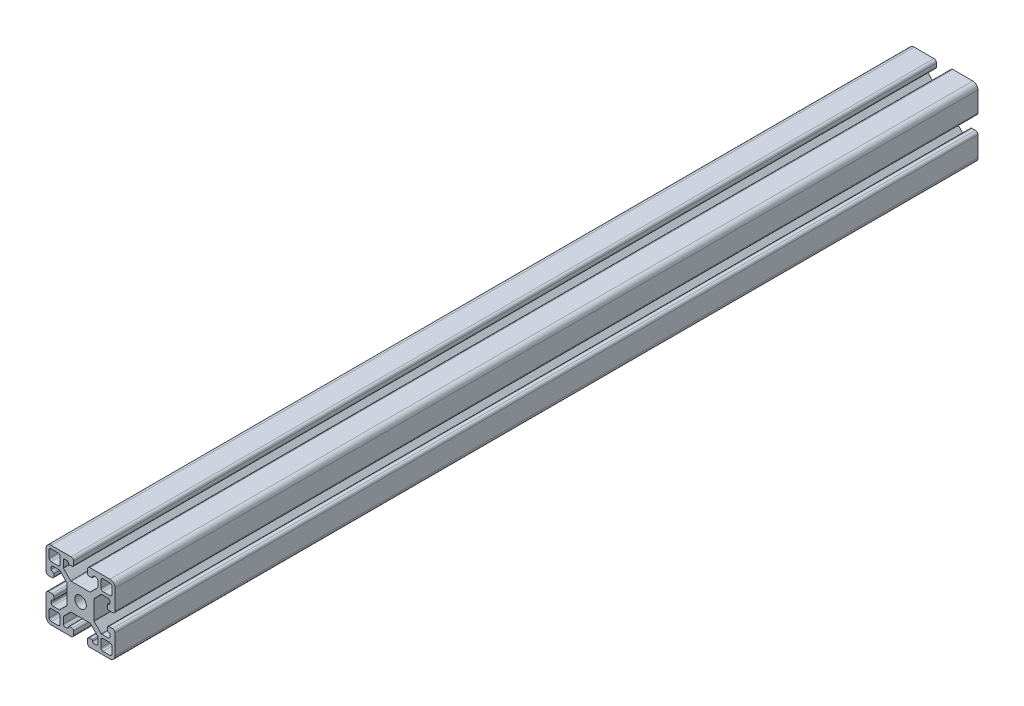
SolidWorks part; units mm, degrees
ref_plane "Front Plane" through (0, 0, 0) normal (0, 0, 1) x (1, 0, 0)
ref_plane "Top Plane" through (0, 0, 0) normal (0, 1, 0) x (1, 0, 0)
ref_plane "Right Plane" through (0, 0, 0) normal (1, 0, 0) x (0, 0, -1)
sketch "Sketch1" plane through (0, 0, 0) normal (0, 0, 1) x (1, 0, 0)
  line B0 (-17, 11.78) -> (-13, 11.78)
  arc B1 (-13, 11.78) -> (-11.78, 13) centre (-13, 13) ccw
  line B2 (-11.78, 13) -> (-11.78, 17)
  arc B3 (-11.78, 17) -> (-13, 18.22) centre (-13, 17) ccw
  line B4 (-13, 18.22) -> (-17, 18.22)
  arc B5 (-17, 18.22) -> (-18.22, 17) centre (-17, 17) ccw
  line B6 (-18.22, 17) -> (-18.22, 13)
  arc B7 (-18.22, 13) -> (-17, 11.78) centre (-17, 13) ccw
  line B8 (-18.22, -13) -> (-18.22, -17)
  arc B9 (-18.22, -17) -> (-17, -18.22) centre (-17, -17) ccw
  line B10 (-17, -18.22) -> (-13, -18.22)
  arc B11 (-13, -18.22) -> (-11.78, -17) centre (-13, -17) ccw
  line B12 (-11.78, -17) -> (-11.78, -13)
  arc B13 (-11.78, -13) -> (-13, -11.78) centre (-13, -13) ccw
  line B14 (-13, -11.78) -> (-17, -11.78)
  arc B15 (-17, -11.78) -> (-18.22, -13) centre (-17, -13) ccw
  line B16 (13, -18.22) -> (17, -18.22)
  arc B17 (17, -18.22) -> (18.22, -17) centre (17, -17) ccw
  line B18 (18.22, -17) -> (18.22, -13)
  arc B19 (18.22, -13) -> (17, -11.78) centre (17, -13) ccw
  line B20 (17, -11.78) -> (13, -11.78)
  arc B21 (13, -11.78) -> (11.78, -13) centre (13, -13) ccw
  line B22 (11.78, -13) -> (11.78, -17)
  arc B23 (11.78, -17) -> (13, -18.22) centre (13, -17) ccw
  line B24 (18.22, 13) -> (18.22, 17)
  arc B25 (18.22, 17) -> (17, 18.22) centre (17, 17) ccw
  line B26 (17, 18.22) -> (13, 18.22)
  arc B27 (13, 18.22) -> (11.78, 17) centre (13, 17) ccw
  line B28 (11.78, 17) -> (11.78, 13)
  arc B29 (11.78, 13) -> (13, 11.78) centre (13, 13) ccw
  line B30 (13, 11.78) -> (17, 11.78)
  arc B31 (17, 11.78) -> (18.22, 13) centre (17, 13) ccw
  line B32 (-9.8536, -11.9786) -> (-5.7714, -7.8964)
  arc B33 (-5.4179, -7.75) -> (-5.7714, -7.8964) centre (-5.4179, -8.25) ccw
  line B34 (-5.4179, -7.75) -> (5.4179, -7.75)
  arc B35 (5.7714, -7.8964) -> (5.4179, -7.75) centre (5.4179, -8.25) ccw
  line B36 (5.7714, -7.8964) -> (9.8536, -11.9786)
  arc B37 (10, -12.3321) -> (9.8536, -11.9786) centre (9.5, -12.3321) ccw
  line B38 (10, -12.3321) -> (10, -16)
  arc B39 (9, -17) -> (10, -16) centre (9, -16) ccw
  line B40 (9, -17) -> (8, -17)
  arc B41 (7, -16) -> (8, -17) centre (8, -16) ccw
  arc B42 (7, -16) -> (6.5, -15.5) centre (6.5, -16) ccw
  line B43 (6.5, -15.5) -> (5, -15.5)
  arc B44 (5, -15.5) -> (4, -16.5) centre (5, -16.5) ccw
  line B45 (4, -16.5) -> (4, -18.5)
  arc B46 (4, -18.5) -> (5.5, -20) centre (5.5, -18.5) ccw
  line B47 (5.5, -20) -> (17, -20)
  arc B48 (17, -20) -> (20, -17) centre (17, -17) ccw
  line B49 (20, -17) -> (20, -5.5)
  arc B50 (20, -5.5) -> (18.5, -4) centre (18.5, -5.5) ccw
  line B51 (18.5, -4) -> (16.5, -4)
  arc B52 (16.5, -4) -> (15.5, -5) centre (16.5, -5) ccw
  line B53 (15.5, -5) -> (15.5, -6.5)
  arc B54 (15.5, -6.5) -> (16, -7) centre (16, -6.5) ccw
  arc B55 (17, -8) -> (16, -7) centre (16, -8) ccw
  line B56 (17, -8) -> (17, -9)
  arc B57 (16, -10) -> (17, -9) centre (16, -9) ccw
  line B58 (16, -10) -> (12.3321, -10)
  arc B59 (11.9786, -9.8536) -> (12.3321, -10) centre (12.3321, -9.5) ccw
  line B60 (11.9786, -9.8536) -> (7.8964, -5.7714)
  arc B61 (7.75, -5.4179) -> (7.8964, -5.7714) centre (8.25, -5.4179) ccw
  line B62 (7.75, -5.4179) -> (7.75, 5.4179)
  arc B63 (7.8964, 5.7714) -> (7.75, 5.4179) centre (8.25, 5.4179) ccw
  line B64 (7.8964, 5.7714) -> (11.9786, 9.8536)
  arc B65 (12.3321, 10) -> (11.9786, 9.8536) centre (12.3321, 9.5) ccw
  line B66 (12.3321, 10) -> (16, 10)
  arc B67 (17, 9) -> (16, 10) centre (16, 9) ccw
  line B68 (17, 9) -> (17, 8)
  arc B69 (16, 7) -> (17, 8) centre (16, 8) ccw
  arc B70 (16, 7) -> (15.5, 6.5) centre (16, 6.5) ccw
  line B71 (15.5, 6.5) -> (15.5, 5)
  arc B72 (15.5, 5) -> (16.5, 4) centre (16.5, 5) ccw
  line B73 (16.5, 4) -> (18.5, 4)
  arc B74 (18.5, 4) -> (20, 5.5) centre (18.5, 5.5) ccw
  line B75 (20, 5.5) -> (20, 17)
  arc B76 (20, 17) -> (17, 20) centre (17, 17) ccw
  line B77 (17, 20) -> (5.5, 20)
  arc B78 (5.5, 20) -> (4, 18.5) centre (5.5, 18.5) ccw
  line B79 (4, 18.5) -> (4, 16.5)
  arc B80 (4, 16.5) -> (5, 15.5) centre (5, 16.5) ccw
  line B81 (5, 15.5) -> (6.5, 15.5)
  arc B82 (6.5, 15.5) -> (7, 16) centre (6.5, 16) ccw
  arc B83 (8, 17) -> (7, 16) centre (8, 16) ccw
  line B84 (8, 17) -> (9, 17)
  arc B85 (10, 16) -> (9, 17) centre (9, 16) ccw
  line B86 (10, 16) -> (10, 12.3321)
  arc B87 (9.8536, 11.9786) -> (10, 12.3321) centre (9.5, 12.3321) ccw
  line B88 (9.8536, 11.9786) -> (5.7714, 7.8964)
  arc B89 (5.4179, 7.75) -> (5.7714, 7.8964) centre (5.4179, 8.25) ccw
  line B90 (5.4179, 7.75) -> (-5.4179, 7.75)
  arc B91 (-5.7714, 7.8964) -> (-5.4179, 7.75) centre (-5.4179, 8.25) ccw
  line B92 (-5.7714, 7.8964) -> (-9.8536, 11.9786)
  arc B93 (-10, 12.3321) -> (-9.8536, 11.9786) centre (-9.5, 12.3321) ccw
  line B94 (-10, 12.3321) -> (-10, 16)
  arc B95 (-9, 17) -> (-10, 16) centre (-9, 16) ccw
  line B96 (-9, 17) -> (-8, 17)
  arc B97 (-7, 16) -> (-8, 17) centre (-8, 16) ccw
  arc B98 (-7, 16) -> (-6.5, 15.5) centre (-6.5, 16) ccw
  line B99 (-6.5, 15.5) -> (-5, 15.5)
  arc B100 (-5, 15.5) -> (-4, 16.5) centre (-5, 16.5) ccw
  line B101 (-4, 16.5) -> (-4, 18.5)
  arc B102 (-4, 18.5) -> (-5.5, 20) centre (-5.5, 18.5) ccw
  line B103 (-5.5, 20) -> (-17, 20)
  arc B104 (-17, 20) -> (-20, 17) centre (-17, 17) ccw
  line B105 (-20, 17) -> (-20, 5.5)
  arc B106 (-20, 5.5) -> (-18.5, 4) centre (-18.5, 5.5) ccw
  line B107 (-18.5, 4) -> (-16.5, 4)
  arc B108 (-16.5, 4) -> (-15.5, 5) centre (-16.5, 5) ccw
  line B109 (-15.5, 5) -> (-15.5, 6.5)
  arc B110 (-15.5, 6.5) -> (-16, 7) centre (-16, 6.5) ccw
  arc B111 (-17, 8) -> (-16, 7) centre (-16, 8) ccw
  line B112 (-17, 8) -> (-17, 9)
  arc B113 (-16, 10) -> (-17, 9) centre (-16, 9) ccw
  line B114 (-16, 10) -> (-12.3321, 10)
  arc B115 (-11.9786, 9.8536) -> (-12.3321, 10) centre (-12.3321, 9.5) ccw
  line B116 (-11.9786, 9.8536) -> (-7.8964, 5.7714)
  arc B117 (-7.75, 5.4179) -> (-7.8964, 5.7714) centre (-8.25, 5.4179) ccw
  line B118 (-7.75, 5.4179) -> (-7.75, -5.4179)
  arc B119 (-7.8964, -5.7714) -> (-7.75, -5.4179) centre (-8.25, -5.4179) ccw
  line B120 (-7.8964, -5.7714) -> (-11.9786, -9.8536)
  arc B121 (-12.3321, -10) -> (-11.9786, -9.8536) centre (-12.3321, -9.5) ccw
  line B122 (-12.3321, -10) -> (-16, -10)
  arc B123 (-17, -9) -> (-16, -10) centre (-16, -9) ccw
  line B124 (-17, -9) -> (-17, -8)
  arc B125 (-16, -7) -> (-17, -8) centre (-16, -8) ccw
  arc B126 (-16, -7) -> (-15.5, -6.5) centre (-16, -6.5) ccw
  line B127 (-15.5, -6.5) -> (-15.5, -5)
  arc B128 (-15.5, -5) -> (-16.5, -4) centre (-16.5, -5) ccw
  line B129 (-16.5, -4) -> (-18.5, -4)
  arc B130 (-18.5, -4) -> (-20, -5.5) centre (-18.5, -5.5) ccw
  line B131 (-20, -5.5) -> (-20, -17)
  arc B132 (-20, -17) -> (-17, -20) centre (-17, -17) ccw
  line B133 (-17, -20) -> (-5.5, -20)
  arc B134 (-5.5, -20) -> (-4, -18.5) centre (-5.5, -18.5) ccw
  line B135 (-4, -18.5) -> (-4, -16.5)
  arc B136 (-4, -16.5) -> (-5, -15.5) centre (-5, -16.5) ccw
  line B137 (-5, -15.5) -> (-6.5, -15.5)
  arc B138 (-6.5, -15.5) -> (-7, -16) centre (-6.5, -16) ccw
  arc B139 (-8, -17) -> (-7, -16) centre (-8, -16) ccw
  line B140 (-8, -17) -> (-9, -17)
  arc B141 (-10, -16) -> (-9, -17) centre (-9, -16) ccw
  line B142 (-10, -16) -> (-10, -12.3321)
  arc B143 (-9.8536, -11.9786) -> (-10, -12.3321) centre (-9.5, -12.3321) ccw
  circle B144 centre (0, 0) radius 3.35
sketch_block_instance "S8-4040 - S-1"
sketch_block "S8-4040 - S"
extrude "Boss-Extrude1" add sketch "Sketch1" along normal blind 500
